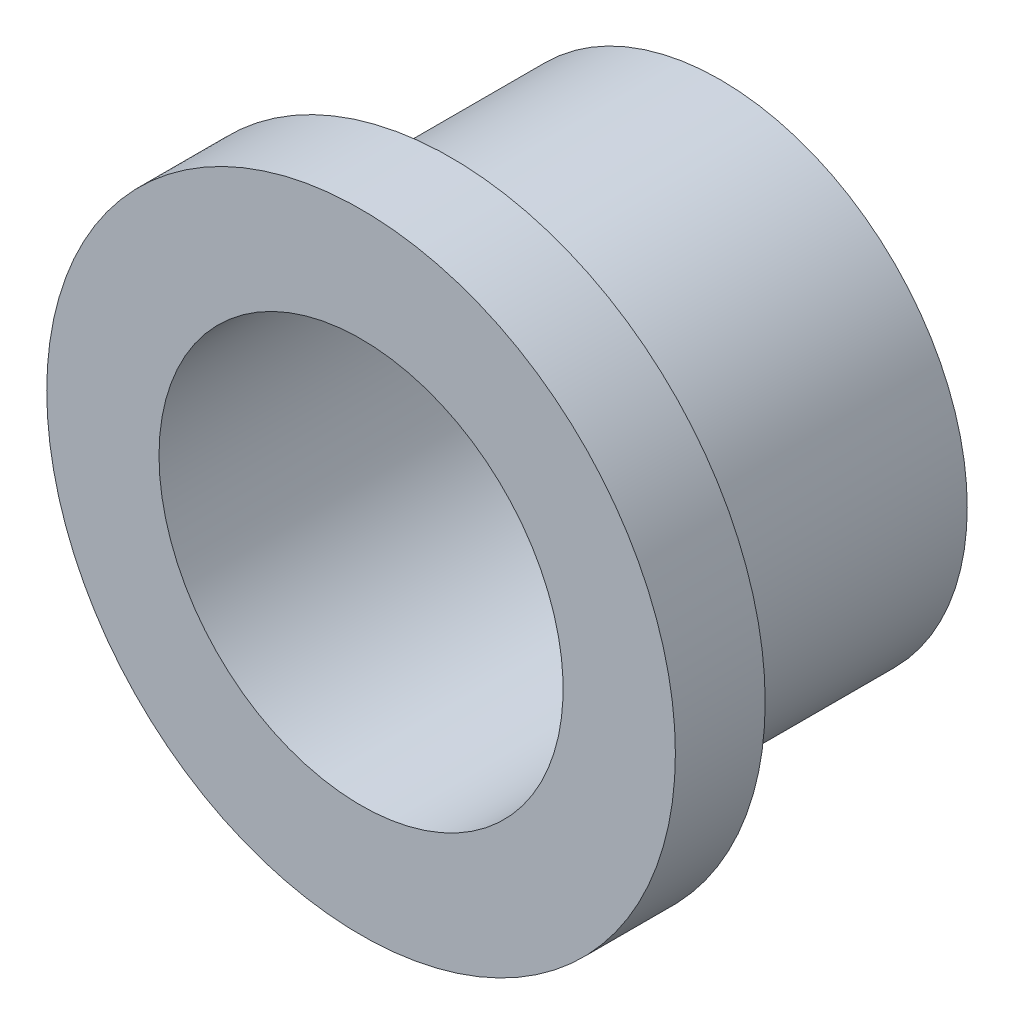
SolidWorks part; units mm, degrees
ref_plane "Front Plane" through (0, 0, 0) normal (0, 0, 1) x (1, 0, 0)
ref_plane "Top Plane" through (0, 0, 0) normal (0, 1, 0) x (1, 0, 0)
ref_plane "Right Plane" through (0, 0, 0) normal (1, 0, 0) x (0, 0, -1)
sketch "Sketch2" plane through (0, 0, 0) normal (0, 0, 1) x (1, 0, 0)
  circle A0 centre (0, 0) radius 27.5
  circle A1 centre (0, 0) radius 22.5
  dimension "D1" = 55
  dimension "D2" = 45
extrude "Boss-Extrude2" add sketch "Sketch2" along normal mid plane 30
sketch "Sketch3" plane through (0, 0, 15) normal (0, 0, 1) x (1, 0, 0)
  circle A0 centre (0, 0) radius 35
  dimension "D1" = 70
extrude "Boss-Extrude3" add sketch "Sketch3" along normal blind 10
sketch "Sketch4" plane through (0, 0, 15) normal (0, 0, -1) x (-1, 0, 0)
  circle A0 centre (0, 0) radius 22.5 construction
  circle A1 centre (0, 0) radius 22.5
extrude "Cut-Extrude1" cut sketch "Sketch4" against normal through all both and the other way through all
